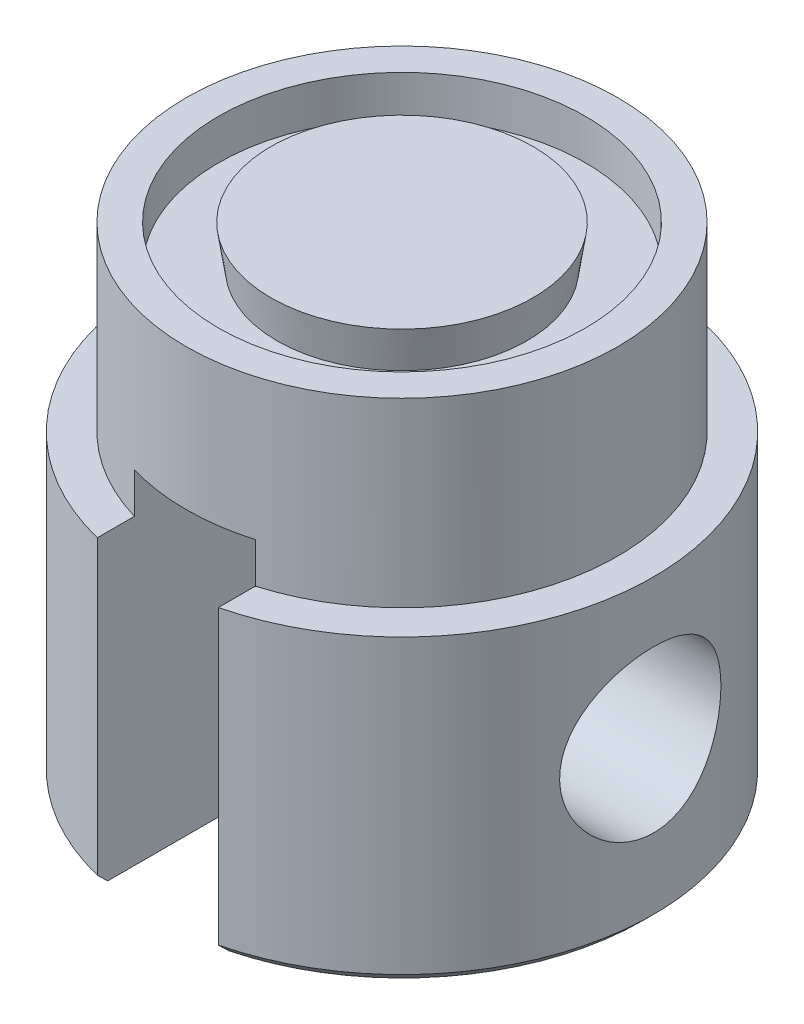
SolidWorks part; units mm, degrees
material "Brass"
ref_plane "Front Plane" through (0, 0, 0) normal (0, 0, 1) x (1, 0, 0)
ref_plane "Top Plane" through (0, 0, 0) normal (0, 1, 0) x (1, 0, 0)
ref_plane "Right Plane" through (0, 0, 0) normal (1, 0, 0) x (0, 0, -1)
sketch "Sketch1" plane through (0, 0, 0) normal (0, 0, 1) x (1, 0, 0)
  line L0 (-9.1, 0) -> (-9.1, -2)
  line L1 (-10.7, 0) -> (-9.1, 0)
  line L2 (-10.7, 0) -> (-10.7, -9)
  line L5 (-12.475, -9) -> (-10.7, -9)
  line L6 (-12.475, -9) -> (-12.475, -24)
  line L7 (-12.475, -24) -> (0, -24)
  line L9 (-9.1, -2) -> (-6.2, -2)
  line L10 (-6.2, -2) -> (-6.5, 0)
  line L11 (0, 0) -> (0, -24)
  line L12 (-6.5, 0) -> (0, 0)
  dimension "D1" = 24
  dimension "D2" = 9
  dimension "D3" = 12.475
  dimension "D4" = 10.7
  dimension "D5" = 2
  dimension "D6" = 2.6
  dimension "D7" = 2.9
  dimension "D8" = 6.5
revolve "Revolve1" add sketch "Sketch1" angle 360 about L11
sketch "Sketch2" plane through (0, 0, 0) normal (0, 0, 1) x (1, 0, 0)
  line L0 (-12.475, -24) -> (12.475, -24) construction
  line L1 (-3, -7) -> (3, -7)
  line L2 (-3, -7) -> (-3, -24)
  line L3 (-3, -24) -> (3, -24)
  line L4 (3, -7) -> (3, -24)
  point P6 (0, -7)
  dimension "D1" = 6
  dimension "D2" = 17
extrude "Cut-Extrude1" cut sketch "Sketch2" against normal through all both and the other way through all
sketch "Sketch3" plane through (0, 0, 0) normal (1, 0, 0) x (0, 0, -1)
  circle A0 centre (0, -16) radius 4
  dimension "D1" = 8
  dimension "D2" = 16
extrude "Cut-Extrude2" cut sketch "Sketch3" against normal through all both and the other way through all
chamfer "Chamfer1" distance 0.5 angle 45 2 edges at (12.475, -24, 0) (-12.475, -24, 0)
